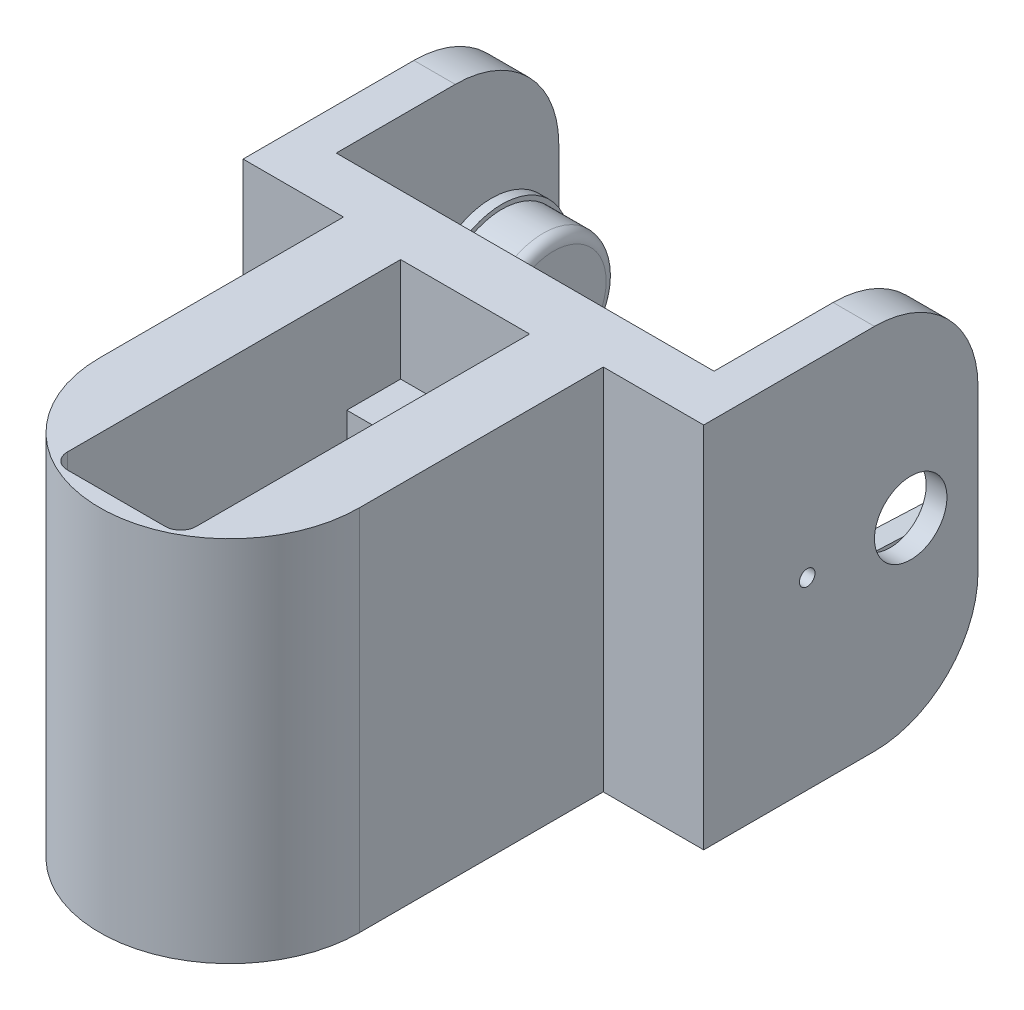
SolidWorks part; units mm, degrees
ref_plane "Front Plane" through (0, 0, 0) normal (0, 0, 1) x (1, 0, 0)
ref_plane "Top Plane" through (0, 0, 0) normal (0, 1, 0) x (1, 0, 0)
ref_plane "Right Plane" through (0, 0, 0) normal (1, 0, 0) x (0, 0, -1)
sketch "Sketch4" plane through (0, 0, 0) normal (0, 0, 1) x (1, 0, 0)
  line L1 (-6.23, -9.975) -> (6.23, -9.975)
  line L2 (-6.23, -9.975) -> (-6.23, 7.275)
  line L3 (-6.23, 7.275) -> (6.23, 7.275)
  line L4 (6.23, -9.975) -> (6.23, 7.275)
  point P4 (0, 7.275)
  dimension "D1" = 12.46
  dimension "D2" = 17.25
  dimension "D3" = 9.975
extrude "Boss-Extrude3" add sketch "Sketch4" along normal blind 6
sketch "Sketch8" plane through (0, -9.975, 0) normal (0, -1, 0) x (-1, 0, 0)
  circle A0 centre (0, -23.55) radius 12.5468
  circle A1 centre (0, -23.55) radius 11.15
  dimension "D1" = 22.3
  dimension "D2" = 23.55
extrude "Boss-Extrude6" add sketch "Sketch8" along normal blind 8.3 and the other way up to surface (17.25 mm away) other way up to face at (0, 7.275, 3)
sketch "Sketch5" plane through (0, 7.275, 0) normal (0, 1, 0) x (1, 0, 0)
  line L8 (12.5468, -23.55) -> (12.5468, 0)
  line L9 (12.5468, 0) -> (6.23, 0)
  line L10 (-12.5468, -23.55) -> (-12.5468, 0)
  line L11 (-12.5468, 0) -> (-6.23, 0)
  line L12 (-6.23, 0) -> (-6.23, -29.7)
  line L14 (6.23, -29.7) -> (6.23, 0)
  line L15 (-6.23, -29.7) -> (6.23, -29.7)
  line L16 (6.23, -6) -> (-6.23, -6) construction
  circle A0 centre (0, -23.55) radius 12.5468 construction
  arc A1 (-12.5468, -23.55) -> (12.5468, -23.55) centre (0, -23.55) ccw
  dimension "D1" = 23.7
  dimension "D2" = 23.55
extrude "Boss-Extrude4" add sketch "Sketch5" against normal up to surface (17.25 mm away) up to face at (0, -9.975, 3)
sketch "Sketch6" plane through (0, 7.275, 0) normal (0, 1, 0) x (1, 0, 0)
  line L0 (6.23, -6) -> (-6.23, -6) construction
  line L3 (6.23, -29.7) -> (-6.23, -29.7) construction
  circle A0 centre (0, -3.6) radius 0.75
  circle A1 centre (0, -32.1) radius 0.75
  dimension "D1" = 1.5
  dimension "D3" = 1.5
  dimension "D2" = 2.4
  dimension "D4" = 2.4
extrude "Cut-Extrude1" cut sketch "Sketch6" against normal blind 5
chamfer "Chamfer1" distance 0.5 angle 60 2 edges at (0, 7.275, 4.35) (0, 7.275, 32.85)
sketch "Sketch10" plane through (0, 7.275, 0) normal (0, 1, 0) x (1, 0, 0)
  line L1 (-6.23, -6) -> (6.23, -6)
  line L2 (-6.23, -6) -> (-6.23, -29.7)
  line L3 (-6.23, -29.7) -> (6.23, -29.7)
  line L4 (6.23, -6) -> (6.23, -29.7)
extrude "Cut-Extrude3" cut sketch "Sketch10" against normal up to surface (17.25 mm away) up to face at (0, -9.975, 10.3399)
ref_plane "Plane1" through (0, 0, 36.0968) normal (0, 0, 1) x (1, 0, 0)
sketch "Sketch13" plane through (0, -18.275, 0) normal (0, -1, 0) x (1, 0, 0)
  line L0 (-12.5468, 23.55) -> (-12.5468, 0)
  line L1 (-12.5468, 0) -> (12.5468, 0)
  line L2 (12.5468, 0) -> (12.5468, 23.55)
  arc A0 (-12.5468, 23.55) -> (12.5468, 23.55) centre (0, 23.55) ccw
  point P3 (0, 0)
extrude "Boss-Extrude7" add sketch "Sketch13" against normal up to surface (8.3 mm away) up to face at (0, -9.975, 10.3399)
sketch "Sketch15" plane through (0, 7.275, 0) normal (0, 1, 0) x (1, 0, 0)
  line L0 (-12.5468, 0) -> (12.5468, 0)
  line L1 (12.5468, 0) -> (12.5468, -23.55)
  line L2 (-12.5468, 0) -> (-12.5468, -23.55)
  line L3 (6.23, -6) -> (6.23, -29.7) construction
  line L4 (-6.23, -0.8) -> (6.23, -0.8)
  line L5 (-6.23, -0.8) -> (-6.23, -33)
  line L6 (-4.73, -34.5) -> (4.73, -34.5)
  line L7 (6.23, -0.8) -> (6.23, -33)
  arc A0 (-12.5468, -23.55) -> (12.5468, -23.55) centre (0, -23.55) ccw
  circle A1 centre (0, -3.6) radius 0.75 construction
  arc A2 (4.73, -34.5) -> (6.23, -33) centre (4.73, -33) ccw
  arc A3 (-6.23, -33) -> (-4.73, -34.5) centre (-4.73, -33) ccw
  point P15 (0, -0.8)
  dimension "D1" = 0.8
  dimension "D3" = 1.5
  dimension "D2" = 2.8
  dimension "D4" = 0
  dimension "D5" = 34.5
extrude "Boss-Extrude9" add sketch "Sketch15" along normal blind 10
sketch "Sketch20" plane through (0, -18.275, 0) normal (0, -1, 0) x (1, 0, 0)
  circle A0 centre (0, 23.55) radius 7.15
  circle A1 centre (0, 23.55) radius 11.15
  circle A2 centre (0, 23.55) radius 11.15 construction
  dimension "D1" = 14.3
extrude "Boss-Extrude11" add sketch "Sketch20" against normal up to surface (8.3 mm away) up to face at (0, -9.975, 27.1007)
sketch "Sketch21" plane through (0, -18.275, 0) normal (0, -1, 0) x (1, 0, 0)
  circle A0 centre (0, 23.55) radius 7.15
  circle A1 centre (0, 23.55) radius 10.15
  circle A2 centre (0, 23.55) radius 7.15 construction
  dimension "D1" = 20.3
extrude "Cut-Extrude7" cut sketch "Sketch21" against normal blind 1.3
sketch "Sketch11" plane through (0, 0, 29.7) normal (0, 0, 1) x (1, 0, 0)
  line L1 (-5, -9.975) -> (5, -9.975)
  line L2 (-5, -9.975) -> (-5, -11.975)
  line L3 (-5, -11.975) -> (5, -11.975)
  line L4 (5, -9.975) -> (5, -11.975)
  line L5 (-3.6469, -9.975) -> (3.6469, -9.975) construction
  point P4 (0, -9.975)
  dimension "D1" = 0
  dimension "D2" = 10
  dimension "D3" = 2
extrude "Cut-Extrude4" cut sketch "Sketch11" against normal up to surface (23.7 mm away) up to face at (0, -1.35, 6)
sketch "Sketch25" plane through (0, -18.275, 0) normal (0, -1, 0) x (1, 0, 0)
  line L0 (6.23, 20.0415) -> (6.23, 6) construction
  line L1 (-6.23, 6) -> (6.23, 6)
  line L2 (-6.23, 6) -> (-6.23, 12)
  line L3 (-6.23, 12) -> (6.23, 12)
  line L4 (6.23, 6) -> (6.23, 12)
  dimension "D1" = 6
extrude "Cut-Extrude8" cut sketch "Sketch25" against normal up to next
sketch "Sketch17" plane through (0, 17.275, 0) normal (0, 1, 0) x (1, 0, 0)
  line L0 (22.25, 26.5) -> (22.25, 0)
  line L1 (22.25, 0) -> (-22.25, 0)
  line L2 (-22.25, 0) -> (-22.25, 26.5)
  line L3 (-22.25, 26.5) -> (-18.25, 26.5)
  line L4 (-18.25, 26.5) -> (-18.25, 5)
  line L5 (-18.25, 5) -> (18.25, 5)
  line L6 (18.25, 5) -> (18.25, 26.5)
  line L7 (18.25, 26.5) -> (22.25, 26.5)
  point P2 (0, 5)
  point P10 (0, 0)
  dimension "D1" = 4
  dimension "D2" = 36.5
  dimension "D3" = 0
  dimension "D4" = 26.5
  dimension "D5" = 5
extrude "Boss-Extrude10" add sketch "Sketch17" against normal up to surface (35.55 mm away)
sketch "Sketch18" plane through (18.25, 0, 0) normal (-1, 0, 0) x (0, 0, 1)
  line L0 (-26.5, -18.275) -> (-26.5, 17.275) construction
  line L1 (-26.5, 5.2191) -> (-5, 5.2191)
  line L2 (-26.5, 5.2191) -> (-26.5, -6.2191)
  line L3 (-26.5, -6.2191) -> (-5, -6.2191)
  line L4 (-5, 5.2191) -> (-5, -6.2191)
  line L5 (-5, -18.275) -> (-5, 17.275) construction
  point P6 (-26.5, -0.5)
  point P7 (-26.5, -0.5)
  dimension "D1" = 0
extrude "Cut-Extrude5" cut sketch "Sketch18" against normal blind 2
sketch "Sketch19" plane through (20.25, 0, 0) normal (-1, 0, 0) x (0, 0, 1)
  line L0 (-26.5, -18.275) -> (-26.5, 17.275) construction
  circle A0 centre (-20, -0.5) radius 3.5
  point P4 (-26.5, -0.5)
  dimension "D1" = 7
  dimension "D2" = 6.5
  dimension "D3" = 0
extrude "Cut-Extrude6" cut sketch "Sketch19" against normal through all both and the other way through all
fillet "Fillet1" radius 10 4 edges at (20.25, 17.275, -26.5) (20.25, -18.275, -26.5) (-20.25, 17.275, -26.5) (-20.25, -18.275, -26.5)
ref_plane "Plane2" through (0, 0, 0) normal (1, 0, 0) x (0, 0, -1)
ref_plane "Plane3" through (0, -0.5, 0) normal (0, -1, 0) x (-1, 0, 0)
sketch "Sketch22" plane through (-22.25, 0, 0) normal (-1, 0, 0) x (0, 0, 1)
  circle A0 centre (-20, -0.5) radius 6.5
  dimension "D1" = 13
extrude "Boss-Extrude12" add sketch "Sketch22" against normal blind 5
sketch "Sketch23" plane through (-17.25, 0, 0) normal (1, 0, 0) x (0, 0, -1)
  circle A0 centre (20, -0.5) radius 6.075
  dimension "D1" = 12.15
extrude "Boss-Extrude13" add sketch "Sketch23" along normal blind 5
fillet "Fillet2" radius 1 1 edges at (-12.25, -0.5, -26.075)
sketch "Sketch26" plane through (20.25, 0, 0) normal (-1, 0, 0) x (0, 0, 1)
  line L0 (-5, 2) -> (-20, 2.6585)
  line L1 (-5, -18.275) -> (-5, 17.275) construction
  line L4 (-5, 5.2191) -> (-5, 2)
  line L6 (-26.5, 5.2191) -> (-5, 5.2191)
  line L7 (-20, -3.6585) -> (-5, -3)
  line L8 (-5, -3) -> (-5, -6.2191)
  line L9 (-24.475, -0.5) -> (24.475, -0.5) construction
  line L11 (-26.5, -6.2191) -> (-5, -6.2191)
  line L12 (-20, 2.6585) -> (-26.5, 2.9439)
  line L13 (-20, -3.6585) -> (-26.5, -3.9438)
  line L14 (-26.5, -3.9438) -> (-26.5, -6.2191)
  line L16 (-26.5, 2.9439) -> (-26.5, 5.2191)
  line L18 (-26.5, -8.275) -> (-26.5, 7.275) construction
  circle A0 centre (-20, -0.5) radius 3.5 construction
  dimension "D1" = 5
  dimension "D2" = 2.5
  dimension "D3" = 0
  dimension "D4" = 6.317
  dimension "D5" = 3.1585
  dimension "D6" = 180
  dimension "D7" = 180
extrude "Boss-Extrude14" add sketch "Sketch26" along normal up to surface (2 mm away) up to face at (18.25, 10.8669, -16.3142)
sketch "Sketch27" plane through (22.25, 0, 0) normal (1, 0, 0) x (0, 0, -1)
  line L0 (-24.475, -0.5) -> (24.475, -0.5) construction
  circle A0 centre (10, -0.5) radius 0.75
  circle A1 centre (20, -0.5) radius 3.5 construction
  dimension "D2" = 1.5
  dimension "D1" = 10
extrude "Cut-Extrude9" cut sketch "Sketch27" against normal up to next
